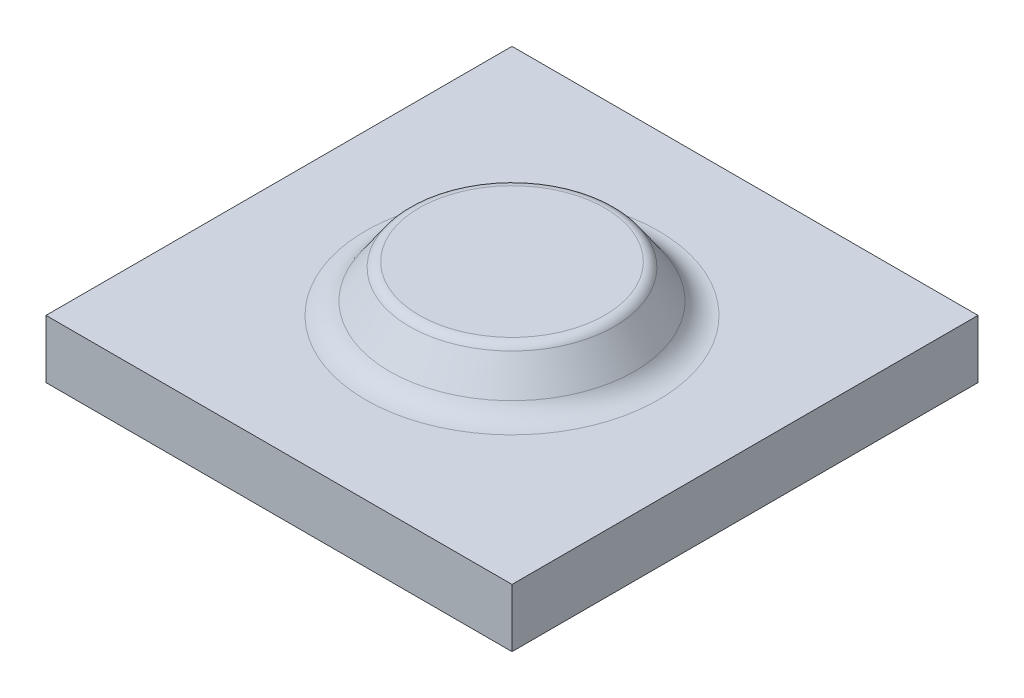
SolidWorks part; units mm, degrees
ref_plane "前视基准面" through (0, 0, 0) normal (0, 0, 1) x (1, 0, 0)
ref_plane "上视基准面" through (0, 0, 0) normal (0, 1, 0) x (1, 0, 0)
ref_plane "右视基准面" through (0, 0, 0) normal (1, 0, 0) x (0, 0, -1)
sketch "草图1" plane through (0, 0, 0) normal (0, 1, 0) x (1, 0, 0)
  line L1 (40, 40) -> (-40, 40)
  line L2 (40, 40) -> (40, -40)
  line L3 (40, -40) -> (-40, -40)
  line L4 (-40, 40) -> (-40, -40)
  line L5 (40, 40) -> (-40, -40) construction
  line L6 (40, -40) -> (-40, 40) construction
  point P0 (0, 0)
  dimension "D1" = 80
extrude "凸台-拉伸1" add sketch "草图1" along normal blind 10
sketch "草图2" plane through (0, 0, 0) normal (0, 0, 1) x (1, 0, 0)
  line L0 (0, 0) -> (0, 24.1175) construction
  line L1 (0, 18) -> (0, 10)
  line L2 (-40, 10) -> (40, 10) construction
  line L3 (0, 10) -> (22.5, 10)
  line L4 (22.5, 10) -> (17, 18)
  line L5 (17, 18) -> (0, 18)
  dimension "D1" = 17
  dimension "D2" = 8
  dimension "D3" = 45
revolve "旋转1" add sketch "草图2" angle 360 about L0
fillet "圆角1" radius 5 1 edges at (0, 10, -22.5)
fillet "圆角2" radius 2 1 edges at (0, 18, -17)
sketch "方向草图" plane through (0, 10, 0) normal (0, 1, 0) x (1, 0, 0)
  line L0 (-40, 40) -> (-40, -40) construction
  line L1 (-40, -40) -> (40, -40) construction
  line L2 (40, -40) -> (40, 40) construction
  line L3 (40, 40) -> (-40, 40) construction
  line L4 (-40, 40) -> (-40, -40) construction
  line L5 (-40, -40) -> (40, -40) construction
  line L6 (40, -40) -> (40, 40) construction
  line L7 (40, 40) -> (-40, 40) construction
  circle A0 centre (0, 0) radius 25.1302 construction
  circle A1 centre (0, 0) radius 25.1302
  point P7 (0, 0)
other "成形工具1"
